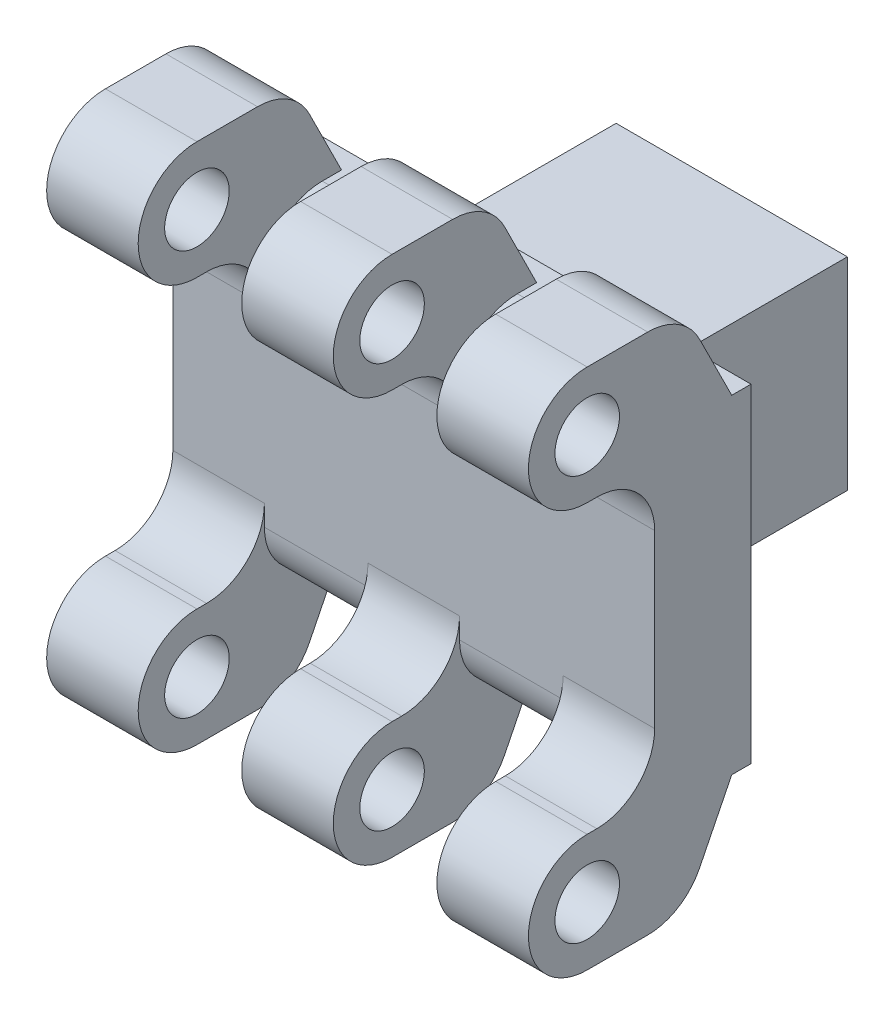
SolidWorks part; units mm, degrees
ref_plane "Front Plane" through (0, 0, 0) normal (0, 0, 1) x (1, 0, 0)
ref_plane "Top Plane" through (0, 0, 0) normal (0, 1, 0) x (1, 0, 0)
ref_plane "Right Plane" through (0, 0, 0) normal (1, 0, 0) x (0, 0, -1)
sketch "Sketch1" plane through (0, 0, 0) normal (0, 0, 1) x (1, 0, 0)
  line L1 (-25, -17.055) -> (25, -17.055)
  line L2 (-25, -17.055) -> (-25, 17.055)
  line L3 (-25, 17.055) -> (25, 17.055)
  line L4 (25, -17.055) -> (25, 17.055)
  line L5 (-25, -17.055) -> (25, 17.055) construction
  line L6 (-25, 17.055) -> (25, -17.055) construction
  point P0 (0, 0)
  dimension "D1" = 50
  dimension "D2" = 34.11
extrude "Boss-Extrude1" add sketch "Sketch1" along normal blind 10
sketch "Sketch3" plane through (0, 0, 0) normal (0, 0, -1) x (-1, 0, 0)
  line L1 (-20.5, -10.5) -> (20.5, -10.5)
  line L2 (-20.5, -10.5) -> (-20.5, 10.5)
  line L3 (-20.5, 10.5) -> (20.5, 10.5)
  line L4 (20.5, -10.5) -> (20.5, 10.5)
  line L5 (-20.5, -10.5) -> (20.5, 10.5) construction
  line L6 (-20.5, 10.5) -> (20.5, -10.5) construction
  point P0 (0, 0)
  dimension "D1" = 41
  dimension "D2" = 21
extrude "Boss-Extrude2" add sketch "Sketch3" along normal blind 3
sketch "Sketch2" plane through (0, 0, 0) normal (0, 0, -1) x (-1, 0, 0)
  line L0 (0, 0) -> (0, -4.7855) construction
  line L1 (-16, -15.5) -> (-12.5, -15.5)
  line L2 (-16, -15.5) -> (-16, 15.5)
  line L3 (-16, 15.5) -> (-12.5, 15.5)
  line L4 (-12.5, -15.5) -> (-12.5, 15.5)
  line L5 (-16, -15.5) -> (-12.5, 15.5) construction
  line L6 (-16, 15.5) -> (-12.5, -15.5) construction
  line L7 (16, 15.5) -> (12.5, 15.5)
  line L8 (12.5, -15.5) -> (12.5, 15.5)
  line L9 (16, -15.5) -> (12.5, -15.5)
  line L10 (16, -15.5) -> (16, 15.5)
  point P0 (-14.25, 0)
  dimension "D1" = 12.5
  dimension "D2" = 3.5
  dimension "D3" = 31
extrude "Cut-Extrude1" cut sketch "Sketch2" against normal blind 7 and the other way through all
sketch "Sketch4" plane through (0, 0, -3) normal (0, 0, -1) x (-1, 0, 0)
  line L0 (12.5, 15.5) -> (12.5, -15.5) construction
  line L1 (-12.5, -10.5) -> (12.5, -10.5)
  line L2 (-12.5, -10.5) -> (-12.5, 10.5)
  line L3 (-12.5, 10.5) -> (12.5, 10.5)
  line L4 (12.5, -10.5) -> (12.5, 10.5)
  line L5 (-12.5, -10.5) -> (12.5, 10.5) construction
  line L6 (-12.5, 10.5) -> (12.5, -10.5) construction
  line L7 (12.5, 10.5) -> (12.5, 15.5) construction
  point P0 (0, 0)
extrude "Boss-Extrude3" add sketch "Sketch4" along normal blind 20
sketch "Sketch5" plane through (0, 0, -23) normal (0, 0, -1) x (-1, 0, 0)
  circle A0 centre (0, 0) radius 8.35
  dimension "D1" = 16.7
extrude "Cut-Extrude2" cut sketch "Sketch5" against normal up to surface (30 mm away) up to face at (-14.25, 0, 7)
sketch "Sketch6" plane through (25, 0, 0) normal (1, 0, 0) x (0, 0, -1)
  line L0 (0, 27.5) -> (0, -27.5) construction
  line L1 (25.355, 0) -> (-25.355, 0) construction
  line L2 (-17, 27.1) -> (-7, 27.1)
  line L3 (-7, 27.1) -> (-2, 17.055)
  line L4 (-10, 17.055) -> (0, 17.055) construction
  line L5 (-17, 14.9) -> (-10, 14.9)
  line L6 (-10, -17.055) -> (-10, 17.055) construction
  line L7 (-10, 14.9) -> (-10, 17.055)
  line L8 (-10, 17.055) -> (-2, 17.055)
  arc A0 (-17, 27.1) -> (-17, 14.9) centre (-17, 21) ccw
  circle A1 centre (-17, 21) radius 3.35
  arc A2 (-17, 14.9) -> (-17, 27.1) centre (-17, 21) ccw construction
  dimension "D1" = 6.7
  dimension "D2" = 12.2
  dimension "D3" = 17
  dimension "D4" = 21
  dimension "D5" = 10
  dimension "D6" = 2
extrude "Boss-Extrude4" add sketch "Sketch6" against normal blind 9.5
pattern_linear "LPattern1" count 3 spacing 20.25 along (-1, 0, 0) of "Boss-Extrude4"
mirror "Mirror1" about plane through (0, 0, 0) normal (0, 1, 0) of "LPattern1", "Boss-Extrude4"
fillet "Fillet1" radius 6 12 edges at (20.25, -27.1, 7) (0, -27.1, 7) (-20.25, -27.1, 7) (20.25, 27.1, 7) (0, 27.1, 7) (-20.25, 27.1, 7) (-20.25, -14.9, 10) (0, -14.9, 10) (20.25, -14.9, 10) (20.25, 14.9, 10) (0, 14.9, 10) (-20.25, 14.9, 10)
sketch "Sketch7" plane through (12.5, 0, 0) normal (1, 0, 0) x (0, 0, -1)
  line L0 (0, 27.5) -> (0, -27.5) construction
  line L1 (23, 10.5) -> (0, 10.5)
  line L2 (23, 10.5) -> (23, -10.5)
  line L3 (23, -10.5) -> (0, -10.5)
  line L4 (0, 10.5) -> (0, -10.5)
  line L5 (3, -10.5) -> (0, -10.5) construction
extrude "Cut-Extrude3" cut sketch "Sketch7" against normal blind 0.5 contours L2 L1 L4 L3
mirror "Mirror2" about plane through (0, 0, 0) normal (1, 0, 0) of "Cut-Extrude3"
fillet "Fillet2" radius 6 4 edges at (10.125, -17.055, 10) (-10.125, -17.055, 10) (-10.125, 17.055, 10) (10.125, 17.055, 10)
